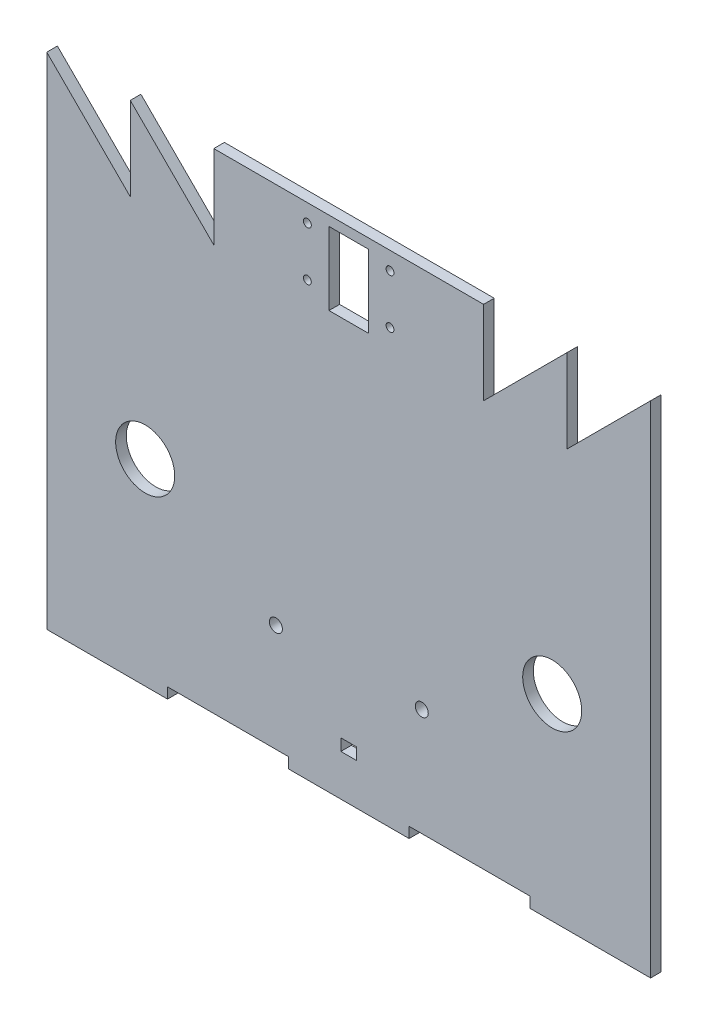
SolidWorks part; units mm, degrees
ref_plane "Ön Düzlem" through (0, 0, 0) normal (0, 0, 1) x (1, 0, 0)
ref_plane "Üst Düzlem" through (0, 0, 0) normal (0, 1, 0) x (1, 0, 0)
ref_plane "Sağ Düzlem" through (0, 0, 0) normal (1, 0, 0) x (0, 0, -1)
sketch "Sketch1" plane through (0, 0, 0) normal (0, 0, 1) x (1, 0, 0)
  line L9 (-2, -17.5) -> (-2, -14.5)
  line L10 (-2, -14.5) -> (2, -14.5)
  line L11 (2, -14.5) -> (2, -17.5)
  line L12 (2, -17.5) -> (-2, -17.5)
  line L21 (-46.02, -28) -> (-46.02, -25.3)
  line L22 (-15.34, -28) -> (-15.34, -25.3)
  line L23 (15.34, -28) -> (15.34, -25.3)
  line L24 (46.02, -28) -> (46.02, -25.3)
  line L33 (-46.02, -28) -> (-76.7, -28)
  line L35 (-15.34, -25.3) -> (-46.02, -25.3)
  line L36 (-15.34, -28) -> (15.34, -28)
  line L37 (15.34, -25.3) -> (46.02, -25.3)
  line L38 (46.02, -28) -> (76.7, -28)
  line L57 (5, 96.5) -> (-5, 96.5)
  line L60 (5, 78) -> (-5, 78)
  line L63 (-5, 78) -> (-5, 96.5)
  line L66 (5, 78) -> (5, 96.5)
  line L67 (34.2736, 99) -> (-34.2736, 99)
  line L68 (-76.7, -28) -> (-76.7, 99)
  line L69 (76.7, -28) -> (76.7, 99)
  line L70 (-76.7, 99) -> (-55.4868, 77.7868)
  line L71 (-55.4868, 77.7868) -> (-55.4868, 99)
  line L72 (-55.4868, 99) -> (-34.2736, 77.7868)
  line L73 (-34.2736, 77.7868) -> (-34.2736, 99)
  line L78 (34.2736, 77.7868) -> (34.2736, 99)
  line L79 (55.4868, 77.7868) -> (55.4868, 99)
  line L80 (76.7, 99) -> (55.4868, 77.7868)
  line L81 (55.4868, 99) -> (34.2736, 77.7868)
  circle A1 centre (-18.5, 2) radius 1.65
  circle A2 centre (18.5679, 2) radius 1.65
  circle A3 centre (-51.7, 22) radius 7.5
  circle A4 centre (51.7, 22) radius 7.5
  circle A9 centre (10.5, 94.5) radius 1
  circle A10 centre (-10.5, 82) radius 1
  circle A11 centre (-10.5, 94.5) radius 1
  circle A12 centre (10.5, 82) radius 1
  point P0 (0, 0)
  point P59 (0, 84.5)
extrude "Boss-Extrude3" add sketch "Sketch1" along normal blind 2.7
